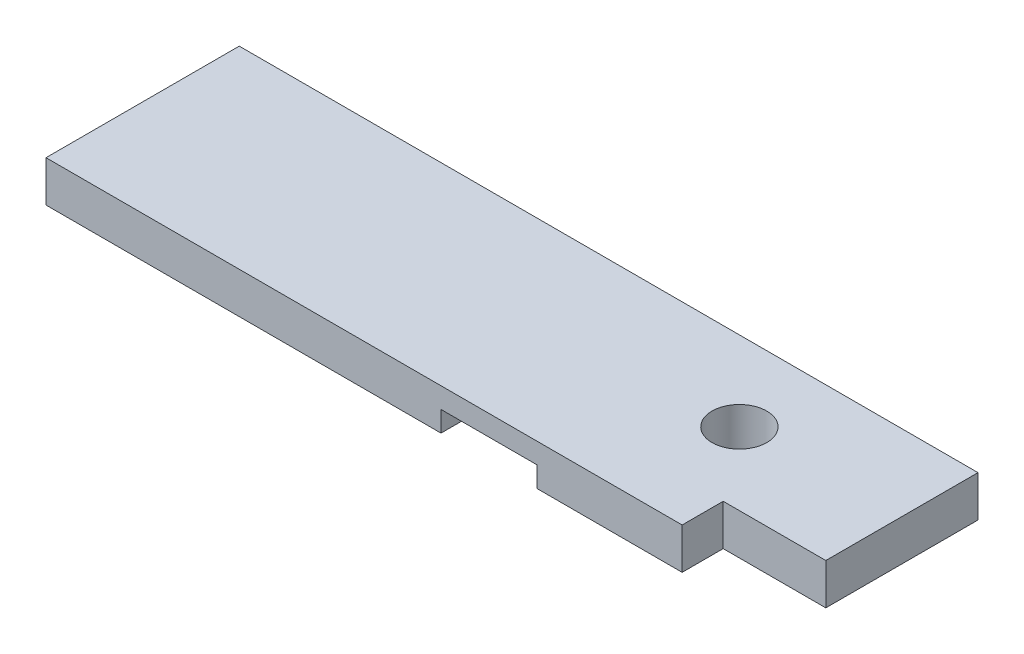
SolidWorks part; units mm, degrees
material "Pine"
ref_plane "Front Plane" through (0, 0, 0) normal (0, 0, 1) x (1, 0, 0)
ref_plane "Top Plane" through (0, 0, 0) normal (0, 1, 0) x (1, 0, 0)
ref_plane "Right Plane" through (0, 0, 0) normal (1, 0, 0) x (0, 0, -1)
sketch "Sketch1" plane through (0, 0, 0) normal (0, 1, 0) x (1, 0, 0)
  line L0 (685.8127, 0) -> (0, 0)
  line L5 (685.8127, 0) -> (685.8127, -141.2875)
  line L6 (590.5627, -179.4002) -> (0, -179.4002)
  line L8 (685.8127, -141.2875) -> (590.5627, -141.2875)
  line L9 (590.5627, -141.2875) -> (590.5627, -179.4002)
  line L10 (0, 0) -> (0, -179.4002)
  circle A0 centre (538.226, -73.9182) radius 25.4
  dimension "D11" = 50.8
  dimension "D2" = 0
  dimension "D3" = 179.4002
  dimension "D4" = 590.5627
  dimension "D5" = 141.2875
  dimension "D6" = 538.226
  dimension "D7" = 73.9182
  dimension "D8" = 685.8127
extrude "Boss-Extrude1" add sketch "Sketch1" along normal blind 38.1
sketch "Sketch2" plane through (0, 0, 0) normal (0, -1, 0) x (1, 0, 0)
  line L0 (0, 179.4002) -> (590.5627, 179.4002) construction
  line L1 (366.701, 179.4002) -> (455.601, 179.4002)
  line L2 (366.701, 179.4002) -> (366.701, 0)
  line L3 (366.701, 0) -> (455.601, 0)
  line L4 (455.601, 179.4002) -> (455.601, 0)
  line L5 (685.8127, 0) -> (0, 0) construction
  dimension "D1" = 88.9
  dimension "D2" = 366.701
extrude "Cut-Extrude1" cut sketch "Sketch2" against normal blind 19.05
